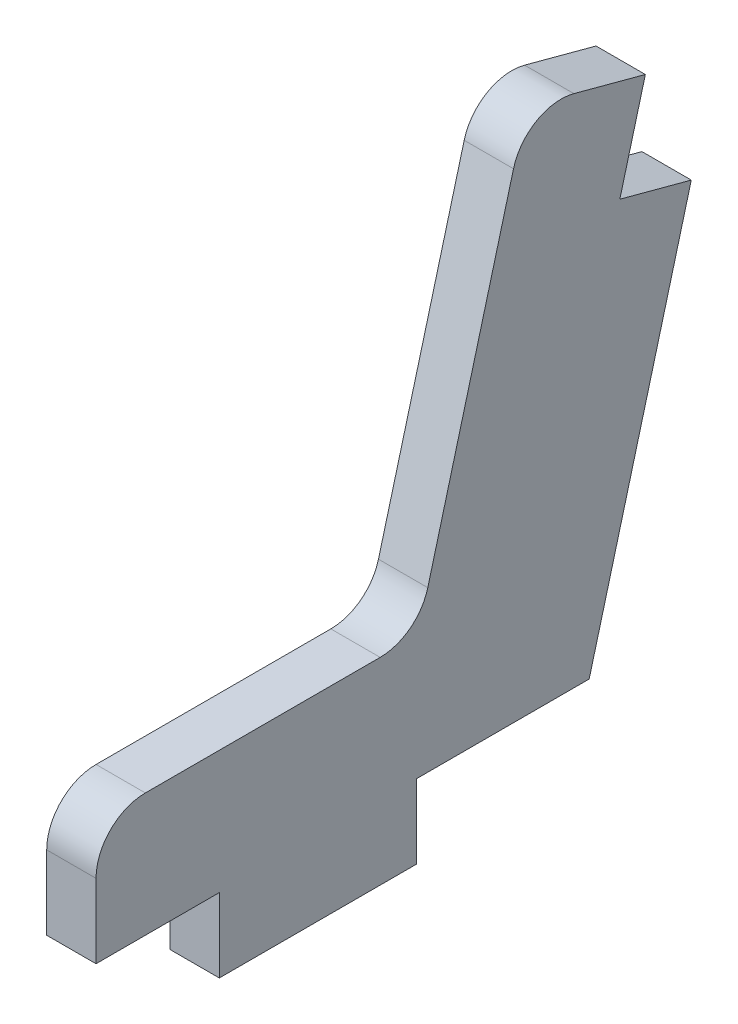
SolidWorks part; units mm, degrees
ref_plane "Plan de face" through (0, 0, 0) normal (0, 0, 1) x (1, 0, 0)
ref_plane "Plan de dessus" through (0, 0, 0) normal (0, 1, 0) x (1, 0, 0)
ref_plane "Plan de droite" through (0, 0, 0) normal (1, 0, 0) x (0, 0, -1)
sketch "Esquisse1" plane through (0, 0, 0) normal (1, 0, 0) x (0, 0, -1)
  line L0 (-20.5004, -12.7052) -> (-15.5004, -12.7052)
  line L1 (-15.5004, -12.7052) -> (-15.5004, -15.7052)
  line L2 (-15.5004, -15.7052) -> (-7.5004, -15.7052)
  line L3 (-7.5004, -15.7052) -> (-7.5004, -12.7052)
  line L4 (-7.5004, -12.7052) -> (-0.5004, -12.7052)
  line L5 (-0.5004, -12.7052) -> (3.6407, 2.7496)
  line L6 (3.6407, 2.7496) -> (0.743, 3.5261)
  line L7 (0.743, 3.5261) -> (1.7782, 7.3898)
  line L8 (1.7782, 7.3898) -> (-3.0514, 8.6838)
  line L9 (-3.0514, 8.6838) -> (-7.4428, -7.7052)
  line L10 (-7.4428, -7.7052) -> (-20.5004, -7.7052)
  line L11 (-20.5004, -7.7052) -> (-20.5004, -12.7052)
  line L12 (-15.5004, -12.7052) -> (-7.5004, -12.7052) construction
  dimension "D1" = 8
  dimension "D2" = 3
  dimension "D3" = 5
  dimension "D4" = 8
  dimension "D5" = 8
  dimension "D6" = 4
  dimension "D7" = 3
  dimension "D8" = 105
  dimension "D9" = 7
  dimension "D10" = 16
  dimension "D11" = 4
extrude "Boss.-Extru.1" add sketch "Esquisse1" along normal blind 2
fillet "Congé1" radius 2 3 edges at (1, 8.6838, 3.0514) (1, -7.7052, 7.4428) (1, -7.7052, 20.5004)
